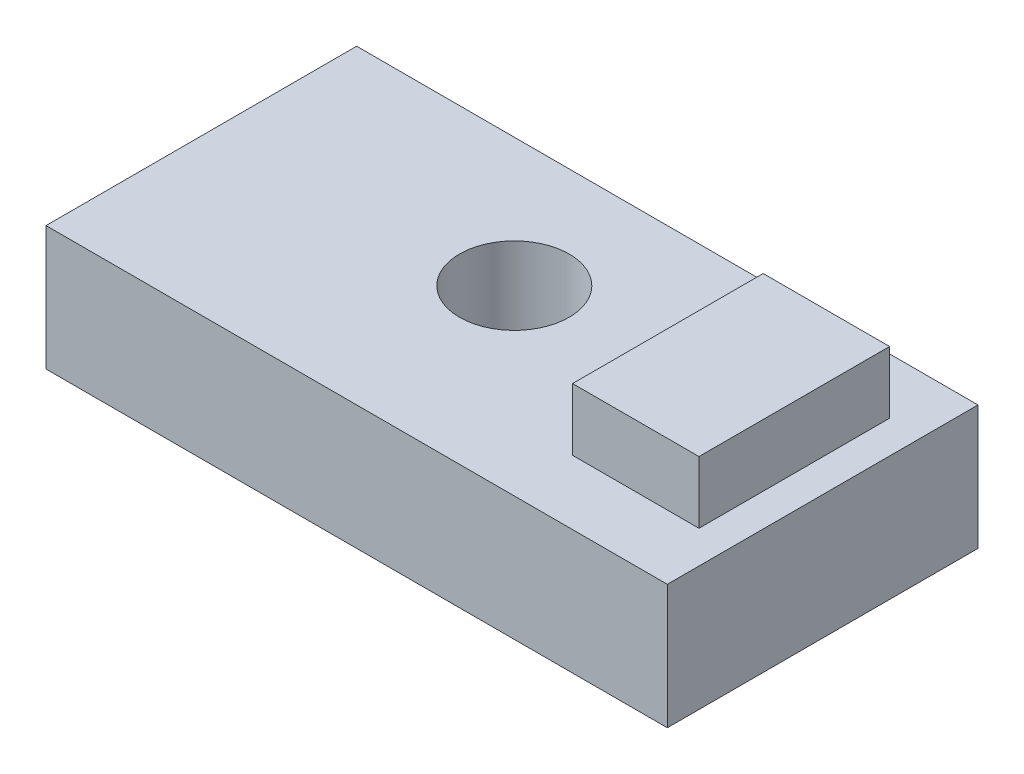
SolidWorks part; units mm, degrees
ref_plane "Front Plane" through (0, 0, 0) normal (0, 0, 1) x (1, 0, 0)
ref_plane "Top Plane" through (0, 0, 0) normal (0, 1, 0) x (1, 0, 0)
ref_plane "Right Plane" through (0, 0, 0) normal (1, 0, 0) x (0, 0, -1)
sketch "Sketch1" plane through (0, 0, 0) normal (0, 1, 0) x (1, 0, 0)
  line L4 (-342.3733, 1128.076) -> (3467.6267, 1128.076)
  line L5 (-342.3733, 1128.076) -> (-342.3733, -776.924)
  line L6 (-342.3733, -776.924) -> (3467.6267, -776.924)
  line L7 (3467.6267, 1128.076) -> (3467.6267, -776.924)
  dimension "D1" = 3810
  dimension "D2" = 1905
extrude "Boss-Extrude1" add sketch "Sketch1" along normal blind 762 contours L5 L4 L7 L6
sketch "Sketch2" plane through (0, 762, 0) normal (0, 1, 0) x (1, 0, 0)
  circle A0 centre (1412.4667, 339.9404) radius 336.2582
extrude "Cut-Extrude1" cut sketch "Sketch2" against normal through all
sketch "Sketch3" plane through (0, 762, 0) normal (0, 1, 0) x (1, 0, 0)
  line L9 (2491.9956, 786.3621) -> (3267.146, 786.3621)
  line L10 (2491.9956, 786.3621) -> (2491.9956, -382.4511)
  line L11 (2491.9956, -382.4511) -> (3267.146, -382.4511)
  line L12 (3267.146, 786.3621) -> (3267.146, -382.4511)
extrude "Boss-Extrude2" add sketch "Sketch3" along normal blind 381
